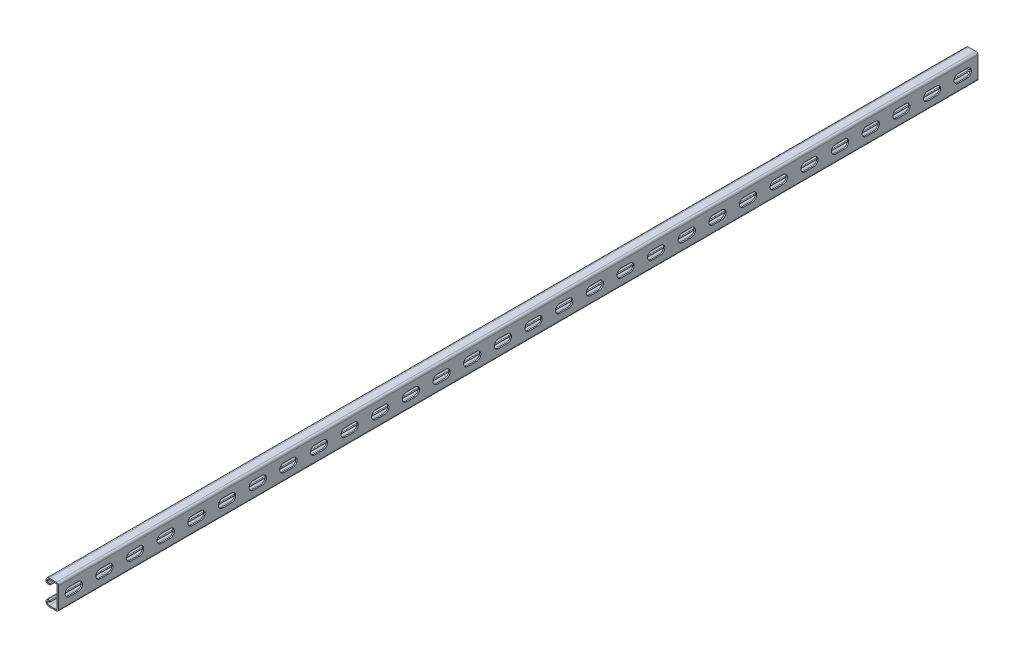
SolidWorks part; units mm, degrees
ref_plane "Front Plane" through (0, 0, 0) normal (0, 0, 1) x (1, 0, 0)
ref_plane "Top Plane" through (0, 0, 0) normal (0, 1, 0) x (1, 0, 0)
ref_plane "Right Plane" through (0, 0, 0) normal (1, 0, 0) x (0, 0, -1)
sketch "Sketch1" plane through (0, 0, 0) normal (0, 0, 1) x (1, 0, 0)
  line L0 (0, 0) -> (-20.6375, 0) construction
  line L3 (-20.6375, 20.6375) -> (0, 20.6375) construction
  line L4 (-20.6375, 20.6375) -> (-20.6375, -20.6375) construction
  line L5 (-20.6375, -20.6375) -> (0, -20.6375) construction
  line L6 (0, 20.6375) -> (0, -20.6375) construction
  line L7 (-15.5892, 20.6375) -> (-3.4607, 20.6375)
  line L8 (0, 17.1767) -> (0, -17.1767)
  line L9 (-2.032, -17.1767) -> (-2.032, 17.1767)
  line L10 (-3.4608, 18.6055) -> (-15.5892, 18.6055)
  line L11 (-20.6375, 15.5892) -> (-20.6375, 14.5732)
  line L12 (-17.1767, 11.1125) -> (-14.5161, 11.1125)
  line L14 (-14.5161, 13.1445) -> (-17.1767, 13.1445)
  line L15 (-18.6055, 14.5732) -> (-18.6055, 15.5892)
  line L16 (-18.6055, -14.5732) -> (-18.6055, -15.5892)
  line L17 (-14.5161, -13.1445) -> (-17.1767, -13.1445)
  line L18 (-17.1767, -11.1125) -> (-14.5161, -11.1125)
  line L19 (-20.6375, -15.5892) -> (-20.6375, -14.5732)
  line L20 (-3.4607, -18.6055) -> (-15.5892, -18.6055)
  line L21 (-15.5892, -20.6375) -> (-3.4607, -20.6375)
  line L22 (-2.032, -20.6375) -> (-2.032, 20.6375) construction
  arc A1 (0, 17.1767) -> (-3.4607, 20.6375) centre (-3.4607, 17.1767) ccw
  arc A2 (-2.032, 17.1767) -> (-3.4608, 18.6055) centre (-3.4607, 17.1767) ccw
  arc A4 (-15.5892, 20.6375) -> (-20.6375, 15.5892) centre (-15.5892, 15.5892) ccw
  arc A5 (-20.6375, 14.5732) -> (-17.1767, 11.1125) centre (-17.1767, 14.5732) ccw
  arc A6 (-14.5161, 11.1125) -> (-14.5161, 13.1445) centre (-14.5161, 12.1285) ccw
  arc A7 (-17.1767, 13.1445) -> (-18.6055, 14.5732) centre (-17.1767, 14.5732) cw
  arc A8 (-18.6055, 15.5892) -> (-15.5892, 18.6055) centre (-15.5892, 15.5892) cw
  arc A9 (-18.6055, -15.5892) -> (-15.5892, -18.6055) centre (-15.5892, -15.5892) ccw
  arc A10 (-17.1767, -13.1445) -> (-18.6055, -14.5732) centre (-17.1767, -14.5732) ccw
  arc A11 (-14.5161, -11.1125) -> (-14.5161, -13.1445) centre (-14.5161, -12.1285) cw
  arc A12 (-20.6375, -14.5732) -> (-17.1767, -11.1125) centre (-17.1767, -14.5732) cw
  arc A13 (-15.5892, -20.6375) -> (-20.6375, -15.5892) centre (-15.5892, -15.5892) cw
  arc A14 (-2.032, -17.1767) -> (-3.4607, -18.6055) centre (-3.4607, -17.1767) cw
  arc A15 (0, -17.1767) -> (-3.4607, -20.6375) centre (-3.4607, -17.1767) cw
  point P24 (0, 20.6375)
  point P65 (-2.032, 0)
  dimension "D1" = 3.4608
  dimension "D2" = 5.0482
  dimension "D3" = 3.4608
  dimension "Ht." = 20.6375
  dimension "Wd." = 41.275
  dimension "Thk." = 2.032
  dimension "D4" = 9.525
  dimension "D5" = 7.1374
extrude "Boss-Extrude1" add sketch "Sketch1" against normal blind 1524
sketch "Sketch3" plane through (0, 0, 0) normal (1, 0, 0) x (0, 0, -1)
  line L0 (0, 0) -> (1524, 0) construction
  point P2 (101.6, 0)
  point P3 (1422.4, 0)
  dimension "D1" = 101.6
  dimension "D2" = 101.6
  dimension "D3" = 1524
sketch "Sketch2" plane through (0, 0, 0) normal (1, 0, 0) x (0, 0, -1)
  line L0 (18.2562, 0) -> (32.5437, 0) construction
  line L1 (18.2562, 7.1437) -> (32.5437, 7.1437)
  line L2 (18.2562, -7.1437) -> (32.5437, -7.1437)
  line L3 (18.2562, 0) -> (0, 0) construction
  line L4 (25.4, 0) -> (76.2, 0) construction
  line L5 (0, -17.1767) -> (0, 17.1767) construction
  arc A0 (18.2562, 7.1437) -> (18.2562, -7.1437) centre (18.2562, 0) ccw
  arc A1 (32.5437, -7.1437) -> (32.5437, 7.1437) centre (32.5437, 0) ccw
  point P3 (25.4, 0)
  dimension "Hole to End" = 11.1125
  dimension "D2" = 25.4
extrude "Cut-Extrude1" cut sketch "Sketch2" against normal up to vertex (2.032 mm away) up to point (-2.032, 0, 0)
pattern_linear "LPattern1" count 30 spacing 50.8 along (0, 0, -1) of "Cut-Extrude1"
ref_plane "Plane1" through (0, 0, -762) normal (0, 0, 1) x (1, 0, 0)
equation "\"D1@LPattern1\" = \"Slot Ctr.@Sketch2\""
equation "\"Hole Count@LPattern1\" = \"Lg.@Boss-Extrude1\" / \"D1@LPattern1\""
equation "\"D3@Sketch3\" = \"Lg.@Boss-Extrude1\""
